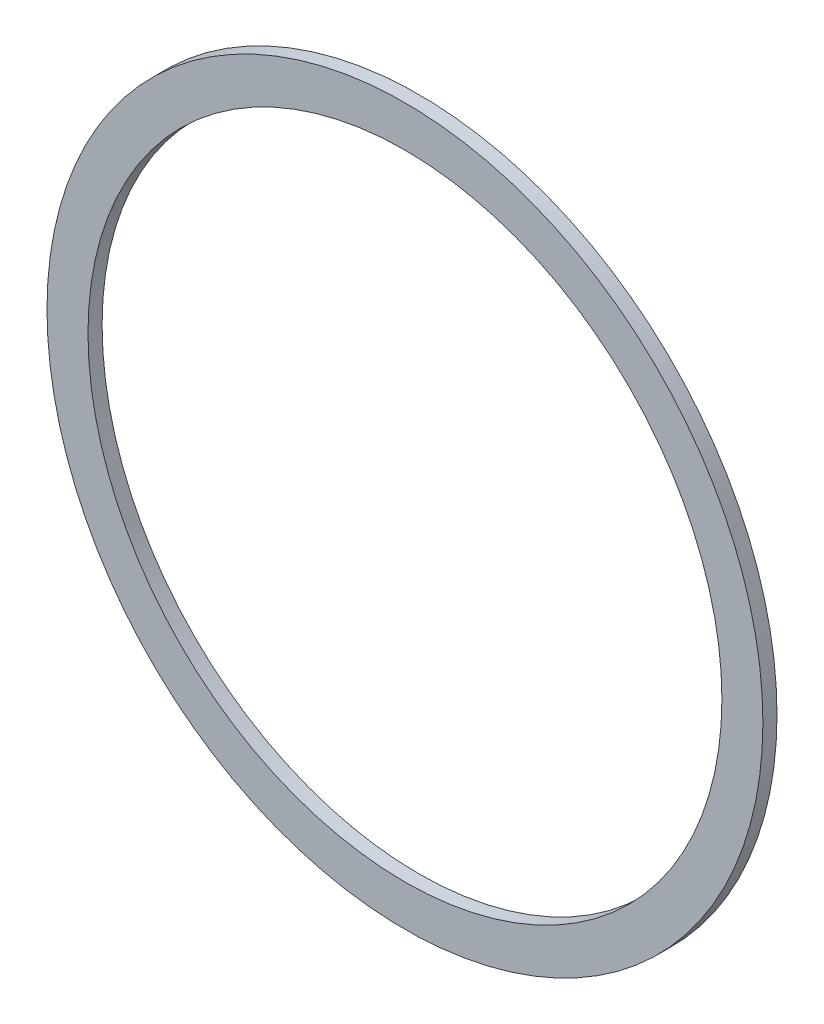
SolidWorks part; units mm, degrees
ref_plane "Front Plane" through (0, 0, 0) normal (0, 0, 1) x (1, 0, 0)
ref_plane "Top Plane" through (0, 0, 0) normal (0, 1, 0) x (1, 0, 0)
ref_plane "Right Plane" through (0, 0, 0) normal (1, 0, 0) x (0, 0, -1)
sketch "Sketch1" plane through (0, 0, 0) normal (0, 0, 1) x (1, 0, 0)
  circle A0 centre (0, 0) radius 101.5
  circle A1 centre (0, 0) radius 89.875
  dimension "D1" = 203
  dimension "D2" = 179.75
extrude "Boss-Extrude1" add sketch "Sketch1" along normal mid plane 4
